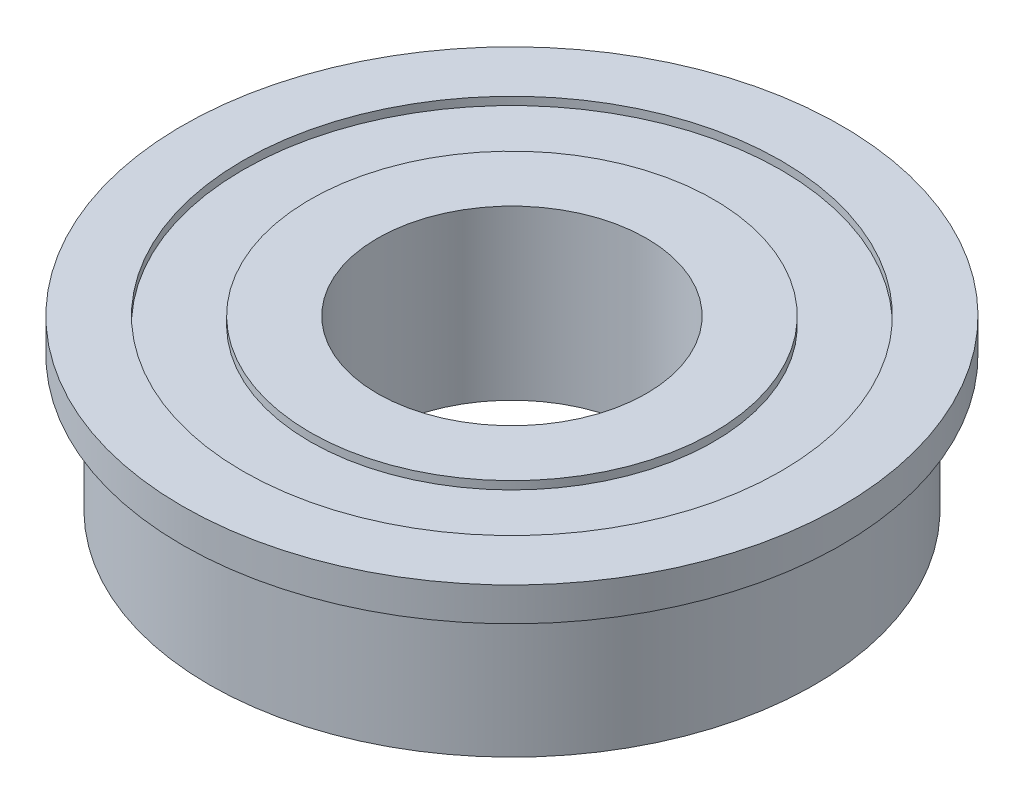
SolidWorks part; units mm, degrees
ref_plane "Front Plane" through (0, 0, 0) normal (0, 0, 1) x (1, 0, 0)
ref_plane "Top Plane" through (0, 0, 0) normal (0, 1, 0) x (1, 0, 0)
ref_plane "Right Plane" through (0, 0, 0) normal (1, 0, 0) x (0, 0, -1)
ref_plane "Plane1" through (0, 0, 0) normal (0, 0, -1) x (-1, 0, 0)
sketch "Sketch1" plane through (0, 0, 0) normal (0, 0, -1) x (-1, 0, 0)
  line L0 (-9.525, 7.5565) -> (-12.7, 7.5565)
  line L1 (-12.7, 7.5565) -> (-12.7, 7.9375)
  line L2 (-12.7, 7.9375) -> (-15.5575, 7.9375)
  line L3 (-15.5575, 7.9375) -> (-15.5575, 6.35)
  line L4 (-15.5575, 6.35) -> (-14.2875, 6.35)
  line L5 (-14.2875, 6.35) -> (-14.2875, 0)
  line L6 (-14.2875, 0) -> (-6.35, 0)
  line L7 (-6.35, 0) -> (-6.35, 7.9375)
  line L8 (-6.35, 7.9375) -> (-9.525, 7.9375)
  line L9 (-9.525, 7.9375) -> (-9.525, 7.5565)
  line L10 (0, 0) -> (0, 7.9375) construction
revolve "Revolve1" add sketch "Sketch1" angle 360 about L10
